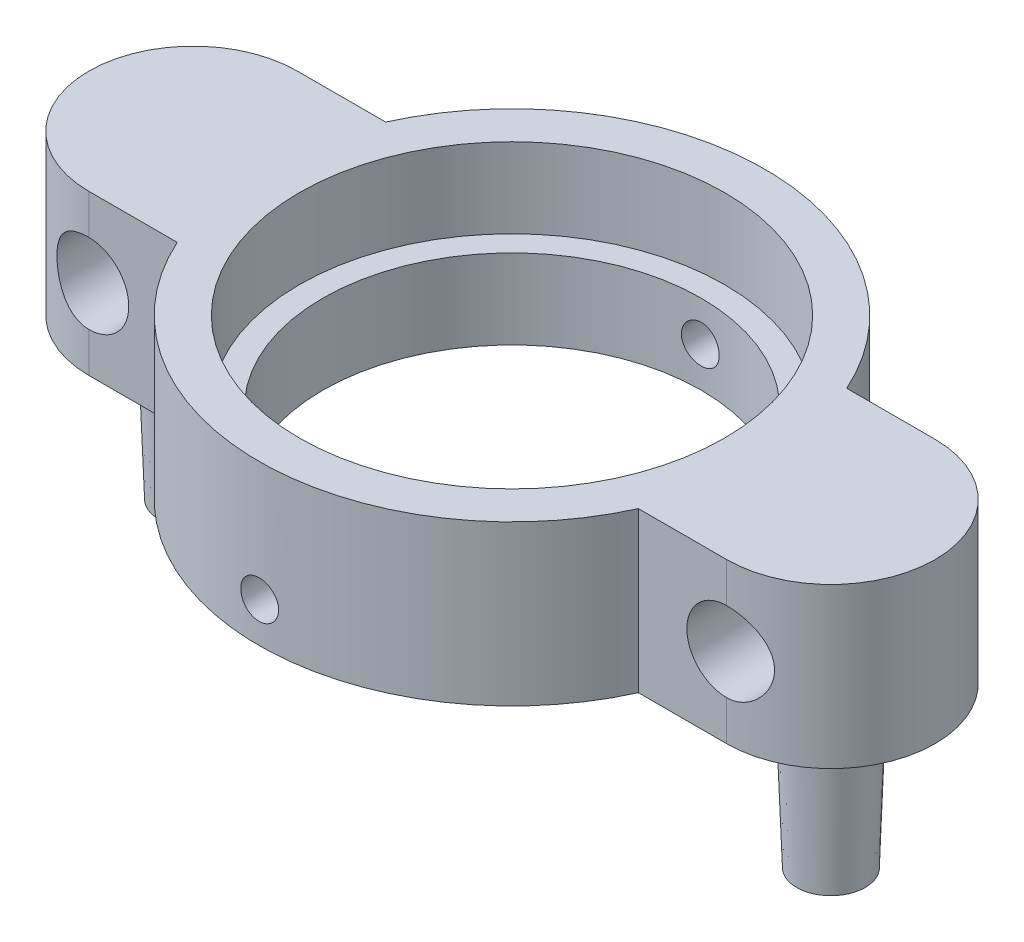
SolidWorks part; units mm, degrees
ref_plane "Front Plane" through (0, 0, 0) normal (0, 0, 1) x (1, 0, 0)
ref_plane "Top Plane" through (0, 0, 0) normal (0, 1, 0) x (1, 0, 0)
ref_plane "Right Plane" through (0, 0, 0) normal (1, 0, 0) x (0, 0, -1)
sketch "Sketch1" plane through (0, 0, 0) normal (0, 1, 0) x (1, 0, 0)
  line L0 (-19.05, 6.223) -> (-13.7723, 6.223)
  line L1 (19.05, 6.223) -> (13.7723, 6.223)
  line L2 (19.05, -6.223) -> (13.7723, -6.223)
  line L3 (-19.05, -6.223) -> (-13.7723, -6.223)
  circle A0 centre (0, 0) radius 11.303
  circle A1 centre (0, 0) radius 15.113 construction
  circle A2 centre (19.05, 0) radius 2.413 construction
  circle A3 centre (-19.05, 0) radius 2.413 construction
  circle A4 centre (19.05, 0) radius 6.223 construction
  circle A5 centre (-19.05, 0) radius 6.223 construction
  arc A6 (-19.05, 6.223) -> (-19.05, -6.223) centre (-19.05, 0) ccw
  arc A7 (19.05, 6.223) -> (19.05, -6.223) centre (19.05, 0) cw
  arc A8 (-13.7723, 6.223) -> (13.7723, 6.223) centre (0, 0) cw
  arc A9 (-13.7723, -6.223) -> (13.7723, -6.223) centre (0, 0) ccw
  dimension "D1" = 22.606
  dimension "D2" = 3.81
  dimension "D3" = 4.826
  dimension "D4" = 19.05
  dimension "D6" = 3.81
  dimension "D5" = 19.05
extrude "Boss-Extrude1" add sketch "Sketch1" along normal blind 9.525
ref_plane "Plane1" through (0, 0, 15.113) normal (0, 0, 1) x (1, 0, 0)
hole_wizard "#4-40 Tapped Hole1" positions "Sketch3" profile "Sketch4" tap size "#4-40" standard "Ansi Inch" end condition through all
sketch "Sketch3" plane through (0, 0, 15.113) normal (0, 0, 1) x (1, 0, 0)
  line L0 (-13.7723, 0) -> (13.7723, 0) construction
  point P1 (0, 2.3813)
  dimension "D1" = 2.3813
sketch "Sketch4" plane through (0, 2.3813, 15.113) normal (1, 0, 0) x (0, -1, 0)
  line L0 (0, 0) -> (0, 30.226)
  line L1 (0, 30.226) -> (1.1303, 30.226)
  line L2 (1.1303, 30.226) -> (1.1303, 0)
  line L5 (1.1303, 0) -> (0, 0)
  line L11 (0, -6.35) -> (0, 107.95) construction
  dimension "Thread Major Dia." = 2.2606
  dimension "Thru Tap Drill Depth" = 30.226
ref_plane "Plane2" through (25.273, 0, 0) normal (1, 0, 0) x (0, 0, -1)
hole_wizard "#4-40 Tapped Hole3" [suppressed] positions "Sketch8" profile "Sketch9" tap size "#4-40" standard "Ansi Inch"
sketch "Sketch8" plane through (0, 9.525, 0) normal (0, 1, 0) x (-1, 0, 0)
  point P0 (12.7, 0)
  dimension "D1" = 12.7
sketch "Sketch9" plane through (-12.7, 9.525, 0) normal (1, 0, 0) x (0, 0, 1)
  line L0 (0, 0) -> (0, 9.525)
  line L1 (0, 9.525) -> (1.1303, 9.525)
  line L2 (1.1303, 9.525) -> (1.1303, 0)
  line L5 (1.1303, 0) -> (0, 0)
  line L11 (0, -6.35) -> (0, 107.95) construction
  dimension "Thread Major Dia." = 2.2606
  dimension "Thru Tap Drill Depth" = 9.525
pattern_circular "CirPattern1" [suppressed] count 6 over 360
sketch "Sketch10" plane through (0, 0, 0) normal (0, -1, 0) x (1, 0, 0)
  circle A0 centre (-19.05, 0) radius 2.3813
  circle A1 centre (19.05, 0) radius 2.3813
  dimension "D1" = 4.7625
extrude "Boss-Extrude2" add sketch "Sketch10" along normal blind 9.525 draft 2
hole_wizard "3/16 (0.1875) Diameter Hole1" positions "Sketch12" profile "Sketch13" hole size "3/16" standard "Ansi Inch"
sketch "Sketch12" plane through (0, 0, 6.223) normal (0, 0, 1) x (1, 0, 0)
  line L0 (-19.05, 9.525) -> (-19.05, 0) construction
  line L2 (19.05, 9.525) -> (19.05, 0) construction
  point P0 (-19.05, 4.7625)
  point P1 (19.05, 4.7625)
  point P7 (-19.05, 4.7625)
sketch "Sketch13" plane through (-19.05, 4.7625, 6.223) normal (1, 0, 0) x (0, -1, 0)
  line L0 (0, 0) -> (0, 26.8308)
  line L1 (0, 26.8308) -> (2.3812, 25.4)
  line L2 (2.3812, 25.4) -> (2.3812, 0)
  line L5 (2.3812, 0) -> (0, 0)
  line L10 (0, 26.8308) -> (-2.3813, 25.4) construction
  line L11 (0, -6.35) -> (0, 107.95) construction
  dimension "Hole Dia." = 4.7625
  dimension "Hole Depth" = 25.4
  dimension "Drill Angle" = 118
sketch "Sketch14" plane through (0, 9.525, 0) normal (0, 1, 0) x (1, 0, 0)
  circle A0 centre (0, 0) radius 12.7
  dimension "D1" = 25.4
extrude "Cut-Extrude1" cut sketch "Sketch14" against normal blind 4.7625
